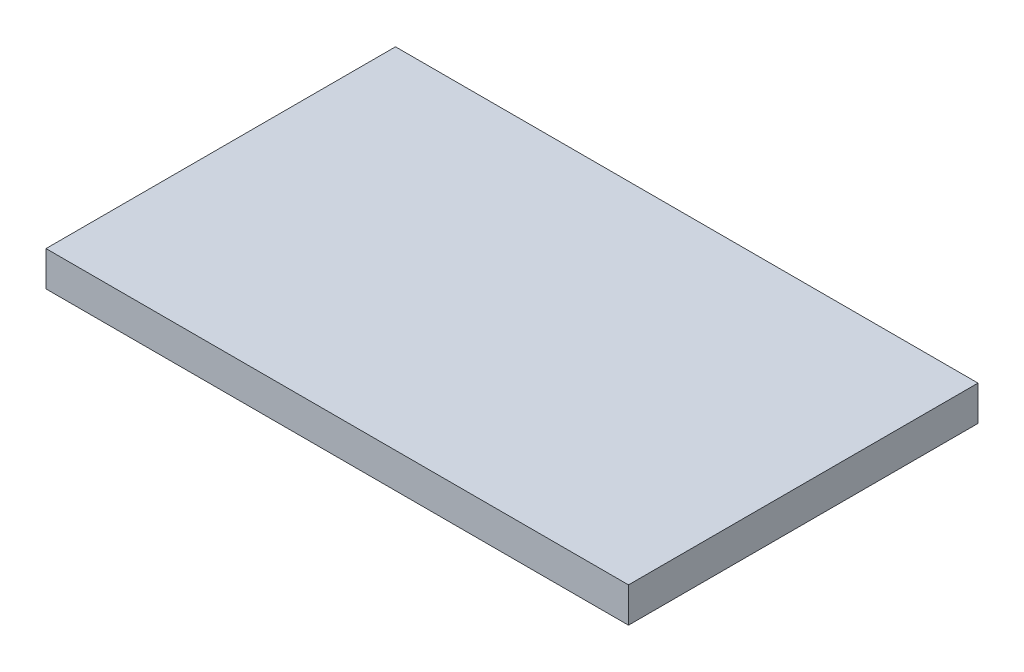
SolidWorks part; units mm, degrees
ref_plane "Front" through (0, 0, 0) normal (0, 0, 1) x (1, 0, 0)
ref_plane "Top" through (0, 0, 0) normal (0, 1, 0) x (1, 0, 0)
ref_plane "Right" through (0, 0, 0) normal (1, 0, 0) x (0, 0, -1)
sketch "Sketch1" plane through (0, 0, 0) normal (0, 1, 0) x (1, 0, 0)
  line L1 (0, 0) -> (10, 0)
  line L2 (0, 0) -> (0, 6)
  line L3 (0, 6) -> (10, 6)
  line L4 (10, 0) -> (10, 6)
  dimension "D1" = 10
  dimension "D2" = 6
extrude "Boss-Extrude1" add sketch "Sketch1" along normal blind 0.6
